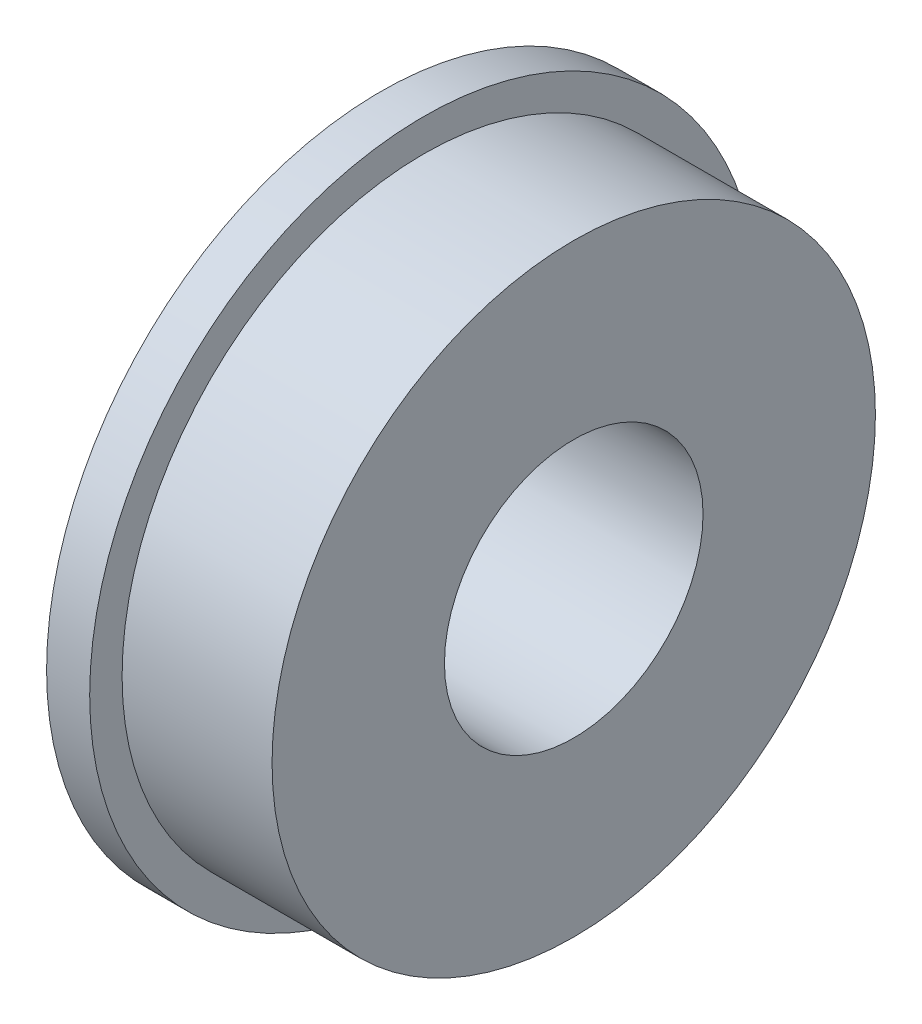
SolidWorks part; units mm, degrees
ref_plane "Front Plane" through (0, 0, 0) normal (0, 0, 1) x (1, 0, 0)
ref_plane "Top Plane" through (0, 0, 0) normal (0, 1, 0) x (1, 0, 0)
ref_plane "Right Plane" through (0, 0, 0) normal (1, 0, 0) x (0, 0, -1)
ref_plane "Plane1" through (0, 0, 0) normal (0, 0, -1) x (-1, 0, 0)
sketch "Sketch1" plane through (0, 0, 0) normal (0, 0, -1) x (-1, 0, 0)
  line L0 (-0.381, 6.35) -> (-0.381, 9.906)
  line L1 (-0.381, 9.906) -> (0, 9.906)
  line L2 (0, 9.906) -> (0, 12.3063)
  line L3 (0, 12.3063) -> (-1.5875, 12.3063)
  line L4 (-1.5875, 12.3063) -> (-1.5875, 11.1125)
  line L5 (-1.5875, 11.1125) -> (-7.112, 11.1125)
  line L6 (-7.112, 11.1125) -> (-7.112, 4.7625)
  line L7 (-7.112, 4.7625) -> (0, 4.7625)
  line L8 (0, 4.7625) -> (0, 6.35)
  line L9 (0, 6.35) -> (-0.381, 6.35)
  line L10 (-7.112, 0) -> (0, 0) construction
revolve "Revolve1" add sketch "Sketch1" angle 360 about L10
